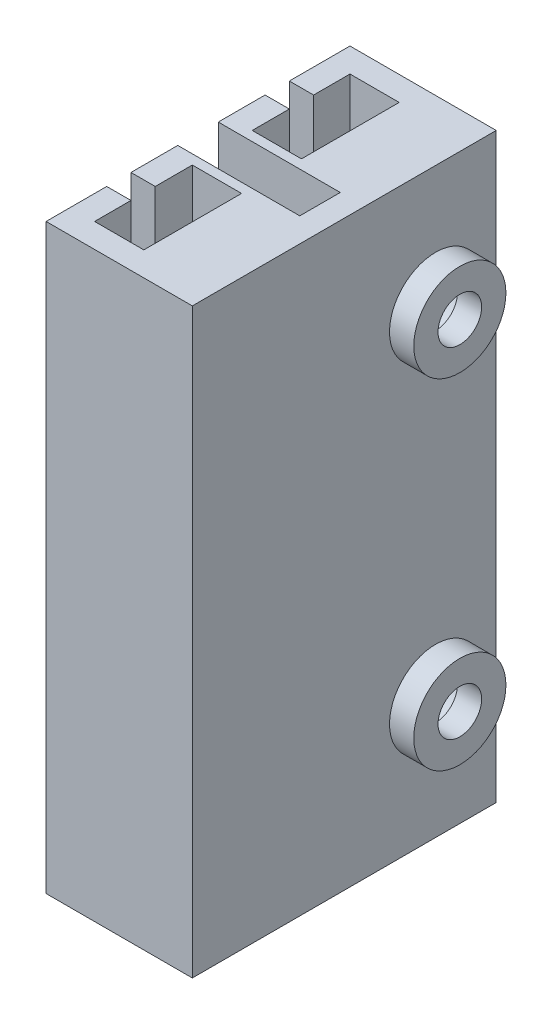
SolidWorks part; units mm, degrees
ref_plane "Front Plane" through (0, 0, 0) normal (0, 0, 1) x (1, 0, 0)
ref_plane "Top Plane" through (0, 0, 0) normal (0, 1, 0) x (1, 0, 0)
ref_plane "Right Plane" through (0, 0, 0) normal (1, 0, 0) x (0, 0, -1)
sketch "Sketch1" plane through (0, 0, 0) normal (0, 1, 0) x (1, 0, 0)
  line L0 (0.7588, 5.315) -> (5, 5.315)
  line L1 (-1.03, 5.315) -> (0.7588, 5.315)
  line L2 (-1.03, 5.315) -> (-1.03, -0.115)
  line L3 (-1.03, -7.215) -> (1.3982, -7.215)
  line L7 (-0.03, 4.315) -> (2, 4.315)
  line L8 (-0.03, 4.315) -> (-0.03, 0.285)
  line L9 (-0.03, 0.285) -> (2, 0.285)
  line L10 (2, 4.315) -> (2, 0.285)
  line L11 (-0.03, -2.185) -> (2, -2.185)
  line L12 (-0.03, -2.185) -> (-0.03, -6.215)
  line L13 (-0.03, -6.215) -> (2, -6.215)
  line L14 (2, -2.185) -> (2, -6.215)
  line L15 (-1.03, -0.115) -> (4, -0.115)
  line L17 (-1.03, -1.785) -> (4, -1.785)
  line L18 (4, -0.115) -> (4, -1.785)
  line L21 (5, 5.315) -> (5, -7.215)
  line L22 (5, -7.215) -> (1.3982, -7.215)
  line L23 (-1.03, -1.785) -> (-1.03, -7.215)
  point P0 (0, 0)
  point P14 (2, -4.2)
  dimension "D1" = 2.03
  dimension "D2" = 4.03
  dimension "D3" = 4.03
  dimension "D4" = 2.03
  dimension "D5" = 6.5
  dimension "D6" = 2
  dimension "D7" = 0
  dimension "D8" = 1
  dimension "D9" = 0.4
  dimension "D10" = 0.4
  dimension "D11" = 1
  dimension "D12" = 1
  dimension "D13" = 1
extrude "Boss-Extrude1" add sketch "Sketch1" along normal blind 24
sketch "Sketch2" plane through (-1.03, 0, 0) normal (-1, 0, 0) x (0, 0, 1)
  line L0 (-5.315, 24) -> (0.115, 24) construction
  line L1 (-2.815, 24) -> (-1.815, 24)
  line L2 (-2.815, 24) -> (-2.815, 0)
  line L3 (-2.815, 0) -> (-1.815, 0)
  line L4 (-1.815, 24) -> (-1.815, 0)
  line L5 (-5.315, 0) -> (0.115, 0) construction
  line L6 (1.785, 24) -> (7.215, 24) construction
  line L7 (3.715, 24) -> (4.715, 24)
  line L8 (3.715, 24) -> (3.715, 0)
  line L9 (3.715, 0) -> (4.715, 0)
  line L10 (4.715, 24) -> (4.715, 0)
  line L11 (1.785, 0) -> (7.215, 0) construction
  line L12 (-5.315, 24) -> (-5.315, 0) construction
  line L13 (7.215, 24) -> (7.215, 0) construction
  dimension "D1" = 1
  dimension "D2" = 1
  dimension "D3" = 2.5
  dimension "D4" = 2.5
extrude "Cut-Extrude1" cut sketch "Sketch2" against normal blind 2
ref_plane "Plane2" through (0, 0, 0.95) normal (0, 0, 1) x (1, 0, 0)
sketch "Sketch3" plane through (5, 0, 0) normal (1, 0, 0) x (0, 0, -1)
  line L0 (5.315, 24) -> (5.315, 0) construction
  line L2 (-7.215, 0) -> (5.315, 0) construction
  line L3 (-7.215, 24) -> (5.315, 24) construction
  circle A0 centre (2.815, 19) radius 0.9
  circle A1 centre (2.815, 5) radius 0.9
  circle A2 centre (2.815, 19) radius 1.9
  circle A3 centre (2.815, 5) radius 1.9
  dimension "D1" = 1.8
  dimension "D2" = 1.8
  dimension "D5" = 5
  dimension "D6" = 5
  dimension "D7" = 1
  dimension "D8" = 1
  dimension "D3" = 2.5
  dimension "D4" = 2.5
extrude "Boss-Extrude2" add sketch "Sketch3" along normal blind 1
sketch "Sketch4" plane through (5, 0, 0) normal (1, 0, 0) x (0, 0, -1)
  circle A0 centre (2.815, 19) radius 1.15
  circle A1 centre (2.815, 5) radius 1.15
extrude "Cut-Extrude2" cut sketch "Sketch4" against normal blind 4
